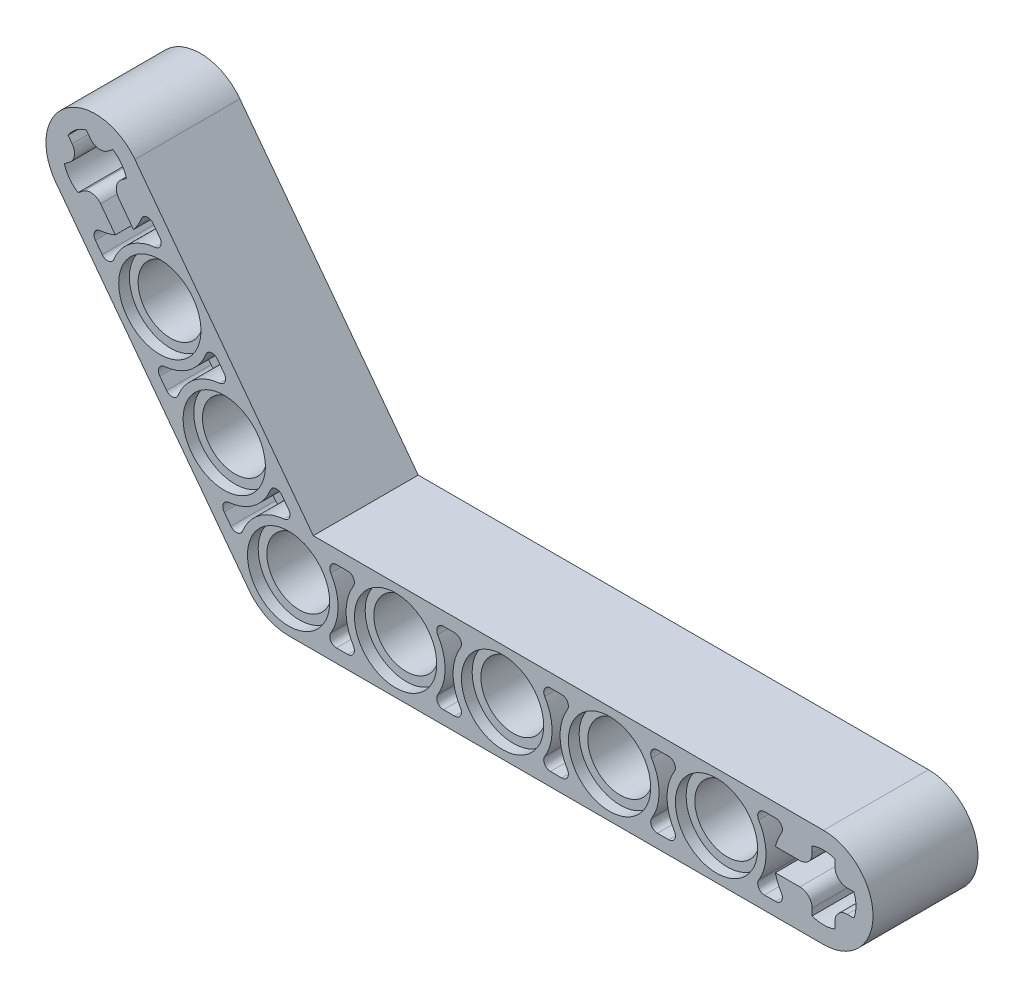
SolidWorks part; units mm, degrees
material "ABS"
ref_plane "Zero X (Front)" through (0, 0, 0) normal (0, 0, 1) x (1, 0, 0)
ref_plane "Zero Z (Top)" through (0, 0, 0) normal (0, 1, 0) x (1, 0, 0)
ref_plane "Zero Y(Right)" through (0, 0, 0) normal (1, 0, 0) x (0, 0, -1)
sketch "Sketch2" plane through (0, 0, 0) normal (0, 0, 1) x (1, 0, 0)
  line L0 (0, -3.7) -> (8, -3.7)
  line L3 (0, 3.7) -> (8, 3.7)
  line L4 (3.5777, 2.7) -> (4.4223, 2.7)
  line L5 (3.5777, -2.7) -> (4.4223, -2.7)
  line L6 (0, 0) -> (8, 0) construction
  arc A1 (3.1518, -1.9381) -> (3.1518, 1.9381) centre (0, 0) ccw
  arc A2 (4.8482, 1.9381) -> (4.8482, -1.9381) centre (8, 0) ccw
  arc A3 (3.1518, 1.9381) -> (3.5777, 2.7) centre (3.5777, 2.2) cw
  arc A4 (4.8482, -1.9381) -> (4.4223, -2.7) centre (4.4223, -2.2) cw
  arc A5 (4.8482, 1.9381) -> (4.4223, 2.7) centre (4.4223, 2.2) ccw
  arc A6 (3.5777, -2.7) -> (3.1518, -1.9381) centre (3.5777, -2.2) cw
  arc A7 (8, -3.7) -> (8, 3.7) centre (8, 0) ccw
  arc A8 (0, 3.7) -> (0, -3.7) centre (0, 0) ccw
  dimension "D3" = 0.5
  dimension "D4" = 7.4
  dimension "D1" = 1
  dimension "Lego_Pitch" = 8
extrude "Boss-Extrude1" add sketch "Sketch2" against normal mid plane 7.85 separate body
sketch "Sketch3" plane through (0, 0, 0) normal (0, 0, 1) x (1, 0, 0)
  line L0 (3.5777, -2.7) -> (4.4223, -2.7) construction
  line L1 (3.5777, 2.7) -> (4.4223, 2.7) construction
  line L2 (3.5777, -2.7) -> (4.4223, -2.7)
  line L3 (3.5777, 2.7) -> (4.4223, 2.7)
  arc A0 (4.8482, 1.9381) -> (4.8482, -1.9381) centre (8, 0) ccw construction
  arc A1 (4.4223, -2.7) -> (4.8482, -1.9381) centre (4.4223, -2.2) ccw construction
  arc A4 (4.8482, 1.9381) -> (4.4223, 2.7) centre (4.4223, 2.2) ccw construction
  arc A5 (3.1518, -1.9381) -> (3.5777, -2.7) centre (3.5777, -2.2) ccw construction
  arc A6 (4.8482, 1.9381) -> (4.8482, -1.9381) centre (8, 0) ccw
  arc A7 (4.4223, -2.7) -> (4.8482, -1.9381) centre (4.4223, -2.2) ccw
  arc A8 (3.1518, -1.9381) -> (3.1518, 1.9381) centre (0, 0) ccw construction
  arc A9 (3.5777, 2.7) -> (3.1518, 1.9381) centre (3.5777, 2.2) ccw construction
  arc A10 (4.8482, 1.9381) -> (4.4223, 2.7) centre (4.4223, 2.2) ccw
  arc A12 (3.1518, -1.9381) -> (3.5777, -2.7) centre (3.5777, -2.2) ccw
  arc A13 (3.1518, -1.9381) -> (3.1518, 1.9381) centre (0, 0) ccw
  arc A14 (3.5777, 2.7) -> (3.1518, 1.9381) centre (3.5777, 2.2) ccw
extrude "Boss-Extrude2" add sketch "Sketch3" along normal mid plane 1.2
sketch "Sketch6" plane through (0, 0, 3.925) normal (0, 0, 1) x (1, 0, 0)
  line L0 (0, 0) -> (-4.8145, 6.3891) construction
  line L1 (0, 0) -> (8, 0) construction
  line L2 (0, 0) -> (8, 0) construction
  line L3 (-1.8596, 8.6158) -> (2.955, 2.2267)
  line L4 (-7.7695, 4.1624) -> (-2.955, -2.2267)
  line L5 (-0.5051, 5.1567) -> (0.0032, 4.4822)
  line L6 (-4.8177, 1.9069) -> (-4.3094, 1.2324)
  line L7 (3.5777, -2.7) -> (4.4223, -2.7) construction
  arc A0 (0, 3.7) -> (0, -3.7) centre (0, 0) ccw construction
  arc A1 (3.1518, -1.9381) -> (3.1518, 1.9381) centre (0, 0) ccw construction
  arc A2 (-2.955, -2.2267) -> (2.955, 2.2267) centre (0, 0) ccw
  arc A3 (-0.349, 3.6835) -> (-3.4446, 1.3508) centre (0, 0) ccw
  arc A4 (-4.4656, 2.7056) -> (-1.3699, 5.0383) centre (-4.8145, 6.3891) ccw
  arc A5 (-1.8596, 8.6158) -> (-7.7695, 4.1624) centre (-4.8145, 6.3891) ccw
  circle A6 centre (0, 0) radius 2.7 construction
  arc A7 (-3.4446, 1.3508) -> (-4.3094, 1.2324) centre (-3.9101, 1.5333) cw
  arc A8 (-4.8177, 1.9069) -> (-4.4656, 2.7056) centre (-4.4184, 2.2078) cw
  arc A9 (-1.3699, 5.0383) -> (-0.5051, 5.1567) centre (-0.9044, 4.8558) cw
  arc A10 (0.0032, 4.4822) -> (-0.349, 3.6835) centre (-0.3961, 4.1813) cw
  arc A11 (3.5777, 2.7) -> (3.1518, 1.9381) centre (3.5777, 2.2) ccw construction
  dimension "D1" = 127
extrude "Boss-Extrude4" add sketch "Sketch6" against normal up to surface (7.85 mm away) up to face at (4, 0, -3.925)
sketch "Sketch7" plane through (0, 0, 0.6) normal (0, 0, 1) x (1, 0, 0)
  line L0 (-0.5051, 5.1567) -> (0.0032, 4.4822) construction
  line L1 (-4.8177, 1.9069) -> (-4.3094, 1.2324) construction
  line L2 (-0.5051, 5.1567) -> (0.0032, 4.4822)
  line L3 (-4.8177, 1.9069) -> (-4.3094, 1.2324)
  arc A0 (-0.349, 3.6835) -> (-3.4446, 1.3508) centre (0, 0) ccw construction
  arc A1 (-0.349, 3.6835) -> (0.0032, 4.4822) centre (-0.3961, 4.1813) ccw construction
  arc A2 (-0.5051, 5.1567) -> (-1.3699, 5.0383) centre (-0.9044, 4.8558) ccw construction
  arc A3 (-4.4656, 2.7056) -> (-1.3699, 5.0383) centre (-4.8145, 6.3891) ccw construction
  arc A4 (-4.4656, 2.7056) -> (-4.8177, 1.9069) centre (-4.4184, 2.2078) ccw construction
  arc A5 (-4.3094, 1.2324) -> (-3.4446, 1.3508) centre (-3.9101, 1.5333) ccw construction
  arc A6 (-0.349, 3.6835) -> (-3.4446, 1.3508) centre (0, 0) ccw
  arc A7 (-0.349, 3.6835) -> (0.0032, 4.4822) centre (-0.3961, 4.1813) ccw
  arc A8 (-0.5051, 5.1567) -> (-1.3699, 5.0383) centre (-0.9044, 4.8558) ccw
  arc A9 (-4.4656, 2.7056) -> (-1.3699, 5.0383) centre (-4.8145, 6.3891) ccw
  arc A10 (-4.4656, 2.7056) -> (-4.8177, 1.9069) centre (-4.4184, 2.2078) ccw
  arc A11 (-4.3094, 1.2324) -> (-3.4446, 1.3508) centre (-3.9101, 1.5333) ccw
extrude "Boss-Extrude5" add sketch "Sketch7" against normal up to surface (1.2 mm away) up to face at (4, 0, -0.6)
sketch "Sketch1" plane through (0, 0, 0) normal (0, 1, 0) x (1, 0, 0)
  line L0 (0, 2.425) -> (0, -2.425) construction
  line L1 (0, 3.925) -> (0, -3.925)
  line L2 (0, -3.925) -> (-3.075, -3.925)
  line L3 (-3.075, -3.925) -> (-3.075, -3.125)
  line L4 (-3.075, -3.125) -> (-2.425, -3.125)
  line L5 (-2.425, -3.125) -> (-2.425, 3.125)
  line L6 (-2.425, 3.125) -> (-3.075, 3.125)
  line L7 (-3.075, 3.125) -> (-3.075, 3.925)
  line L8 (-3.075, 3.925) -> (0, 3.925)
  line L9 (-1.7975, 0) -> (1.7975, 0) construction
  line L10 (-2.955, -3.925) -> (0, -3.925) construction
  line L11 (0, 3.925) -> (-2.955, 3.925) construction
  circle A0 centre (0, 0) radius 2.425 construction
  dimension "D1" = 4.85
  dimension "D4" = 6.25
  dimension "D5" = 6.15
revolve "Cut-Revolve1" cut sketch "Sketch1" angle 360 about L1
pattern_linear "LPattern1" count 5 spacing 8 along (1, 0, 0) of "Cut-Revolve1", "Boss-Extrude1", "Boss-Extrude2"
sketch "Sketch8" plane through (0, 0, 3.925) normal (0, 0, 1) x (1, 0, 0)
  line L0 (40, 0) -> (32, 0) construction
  line L1 (40.85, 2.2712) -> (40.85, 1.7744)
  line L2 (0, 0) -> (8, 0) construction
  line L3 (39.15, 2.2712) -> (39.15, 1.7744)
  line L4 (36.399, 0.85) -> (38.2256, 0.85)
  line L5 (36.399, -0.85) -> (38.2256, -0.85)
  line L6 (3.5777, -2.7) -> (4.4223, -2.7) construction
  line L7 (3.5777, 2.7) -> (4.4223, 2.7) construction
  line L8 (35.5777, -2.7) -> (36.4223, -2.7)
  line L9 (35.5777, 2.7) -> (36.4223, 2.7)
  line L10 (39.15, -1.7744) -> (39.15, -2.2712)
  line L11 (41.7744, 0.85) -> (42.2712, 0.85)
  line L12 (40.85, -1.7744) -> (40.85, -2.2712)
  line L13 (41.7744, -0.85) -> (42.2712, -0.85)
  circle A0 centre (40, 0) radius 0.85 construction
  arc A1 (39.15, -2.2712) -> (40.85, -2.2712) centre (40, 0) ccw
  circle A2 centre (0, 0) radius 2.425 construction
  arc A3 (35.1518, -1.9381) -> (35.1518, 1.9381) centre (32, 0) ccw
  arc A4 (0, 3.7) -> (0, -3.7) centre (0, 0) ccw construction
  arc A5 (36.8482, 1.9381) -> (36.399, 0.85) centre (40, 0) ccw
  arc A6 (36.8482, -1.9381) -> (36.4223, -2.7) centre (36.4223, -2.2) cw
  arc A7 (35.5777, -2.7) -> (35.1518, -1.9381) centre (35.5777, -2.2) cw
  arc A8 (35.1518, 1.9381) -> (35.5777, 2.7) centre (35.5777, 2.2) cw
  arc A9 (36.4223, 2.7) -> (36.8482, 1.9381) centre (36.4223, 2.2) cw
  arc A10 (3.5777, 2.7) -> (3.1518, 1.9381) centre (3.5777, 2.2) ccw construction
  arc A11 (40.85, 2.2712) -> (39.15, 2.2712) centre (40, 0) ccw
  arc A12 (42.2712, -0.85) -> (42.2712, 0.85) centre (40, 0) ccw
  arc A13 (36.399, -0.85) -> (36.8482, -1.9381) centre (40, 0) ccw
  arc A14 (38.2256, -0.85) -> (39.15, -1.7744) centre (38.2256, -1.7744) cw
  arc A15 (40.85, -1.7744) -> (41.7744, -0.85) centre (41.7744, -1.7744) cw
  arc A16 (41.7744, 0.85) -> (40.85, 1.7744) centre (41.7744, 1.7744) cw
  arc A17 (39.15, 1.7744) -> (38.2256, 0.85) centre (38.2256, 1.7744) cw
  circle A18 centre (40, 0) radius 1.585 construction
  dimension "D1" = 1.7
  dimension "D3" = 3.17
  dimension "D2" = 40
extrude "Cut-Extrude1" cut sketch "Sketch8" against normal through all
pattern_linear "LPattern2" count 3 spacing 8 along (-0.6018, 0.7986, 0) of "Boss-Extrude4", "Cut-Revolve1", "Boss-Extrude5"
sketch "Sketch9" plane through (0, 0, 3.925) normal (0, 0, 1) x (1, 0, 0)
  line L0 (-14.4436, 19.1673) -> (-9.629, 12.7782) construction
  line L1 (-16.7689, 18.4793) -> (-16.3722, 18.7782)
  line L2 (0, 0) -> (-4.8145, 6.3891) construction
  line L3 (-15.7458, 17.1216) -> (-15.3492, 17.4205)
  line L4 (-12.9552, 15.7798) -> (-14.0545, 17.2386)
  line L5 (-11.5976, 16.8029) -> (-12.6968, 18.2617)
  line L6 (-0.5051, 5.1567) -> (0.0032, 4.4822) construction
  line L7 (-4.8177, 1.9069) -> (-4.3094, 1.2324) construction
  line L8 (-9.6258, 17.2604) -> (-10.1341, 17.9349)
  line L9 (-13.9385, 14.0106) -> (-14.4468, 14.6851)
  line L10 (-12.5149, 19.5563) -> (-12.1182, 19.8552)
  line L11 (-16.1903, 20.0728) -> (-16.4892, 20.4695)
  line L12 (-13.538, 20.914) -> (-13.1413, 21.2129)
  line L13 (-14.8326, 21.0959) -> (-15.1315, 21.4926)
  circle A0 centre (-14.4436, 19.1673) radius 0.85 construction
  arc A1 (-12.1182, 19.8552) -> (-13.1413, 21.2129) centre (-14.4436, 19.1673) ccw
  arc A3 (-9.978, 16.4617) -> (-13.0737, 14.1289) centre (-9.629, 12.7782) ccw
  arc A5 (-14.0946, 15.4837) -> (-12.9552, 15.7798) centre (-14.4436, 19.1673) ccw
  arc A6 (-10.9989, 17.8165) -> (-10.1341, 17.9349) centre (-10.5334, 17.634) cw
  arc A7 (-9.6258, 17.2604) -> (-9.978, 16.4617) centre (-10.0252, 16.9594) cw
  arc A8 (-13.0737, 14.1289) -> (-13.9385, 14.0106) centre (-13.5392, 14.3115) cw
  arc A9 (-14.4468, 14.6851) -> (-14.0946, 15.4837) centre (-14.0474, 14.986) cw
  arc A10 (-0.349, 3.6835) -> (-3.4446, 1.3508) centre (0, 0) ccw construction
  arc A11 (-16.7689, 18.4793) -> (-15.7458, 17.1216) centre (-14.4436, 19.1673) ccw
  arc A12 (-15.1315, 21.4926) -> (-16.4892, 20.4695) centre (-14.4436, 19.1673) ccw
  arc A13 (-11.5976, 16.8029) -> (-10.9989, 17.8165) centre (-14.4436, 19.1673) ccw
  arc A14 (-12.6968, 18.2617) -> (-12.5149, 19.5563) centre (-11.9585, 18.818) cw
  arc A15 (-13.538, 20.914) -> (-14.8326, 21.0959) centre (-14.0943, 21.6523) cw
  arc A16 (-16.1903, 20.0728) -> (-16.3722, 18.7782) centre (-16.9286, 19.5165) cw
  arc A17 (-15.3492, 17.4205) -> (-14.0545, 17.2386) centre (-14.7928, 16.6822) cw
  circle A18 centre (-14.4436, 19.1673) radius 1.585 construction
  arc A19 (-0.349, 3.6835) -> (0.0032, 4.4822) centre (-0.3961, 4.1813) ccw construction
  circle A20 centre (0, 0) radius 2.425 construction
  dimension "D1" = 1.7
  dimension "D3" = 3.17
  dimension "D2" = 24
extrude "Cut-Extrude2" cut sketch "Sketch9" against normal through all
equation "\"D3@LPattern1\"=\"Lego_Pitch\""
equation "\"D3@LPattern2\" = \"Lego_Pitch\""
equation "\"D2@Sketch8\"=\"Lego_Pitch\"*\"D1@LPattern1\""
equation "\"D2@Sketch9\"=\"Lego_Pitch\"*\"D1@LPattern2\""
